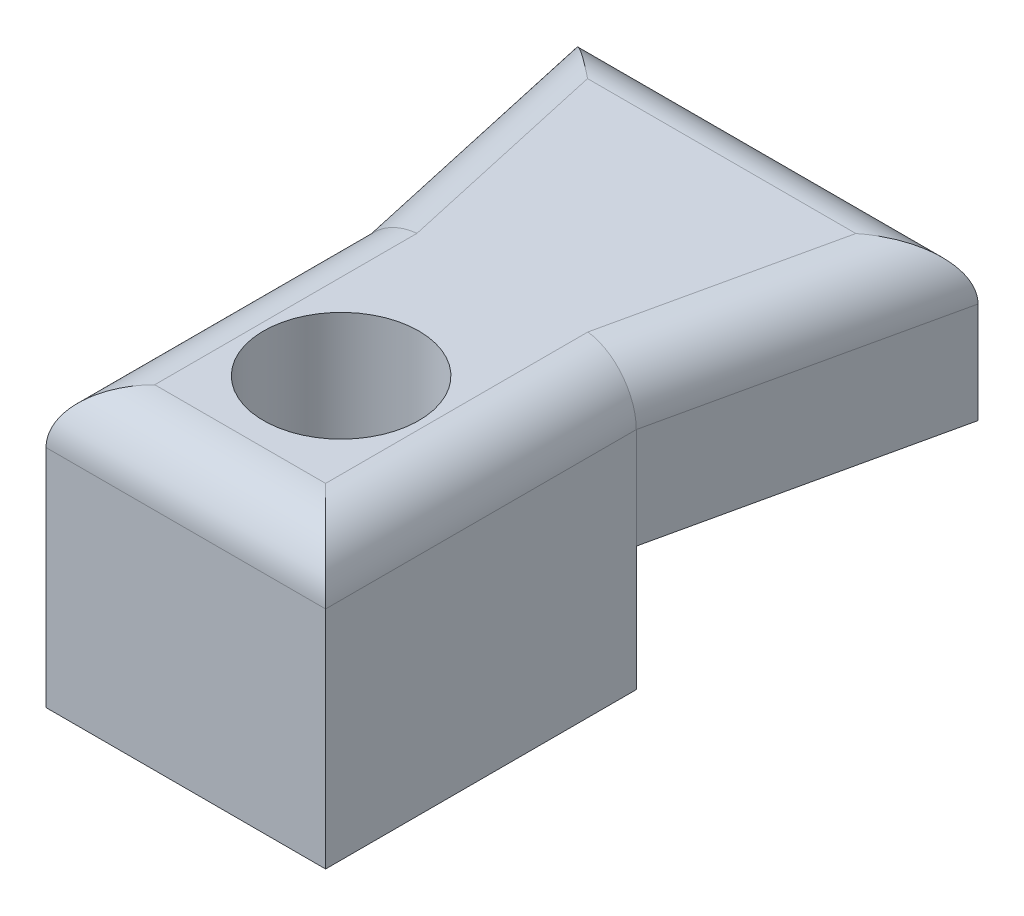
SolidWorks part; units mm, degrees
ref_plane "Front Plane" through (0, 0, 0) normal (0, 0, 1) x (1, 0, 0)
ref_plane "Top Plane" through (0, 0, 0) normal (0, 1, 0) x (1, 0, 0)
ref_plane "Right Plane" through (0, 0, 0) normal (1, 0, 0) x (0, 0, -1)
sketch "Sketch1" plane through (0, 0, 0) normal (0, 1, 0) x (1, 0, 0)
  line L0 (0, 0) -> (-2, 9)
  line L2 (0, 0) -> (0, -10)
  line L3 (0, -10) -> (9, -10)
  line L4 (9, 0) -> (9, -10)
  line L5 (-2, 9) -> (11, 9)
  line L6 (11, 9) -> (9, 0)
  dimension "D1" = 10
  dimension "D2" = 9
  dimension "D3" = 13
  dimension "D4" = 9
extrude "Boss-Extrude2" add sketch "Sketch1" along normal blind 5
sketch "Sketch3" plane through (0, 0, 0) normal (0, -1, 0) x (1, 0, 0)
  line L0 (0, 0) -> (0, 10) construction
  line L1 (9, 0) -> (0, 0)
  line L2 (9, 0) -> (9, 10)
  line L3 (9, 10) -> (0, 10)
  line L4 (0, 0) -> (0, 10)
extrude "Boss-Extrude3" add sketch "Sketch3" along normal blind 4
sketch "Sketch4" plane through (0, -4, 0) normal (0, -1, 0) x (1, 0, 0)
  line L0 (0, 0) -> (9, 10) construction
  circle A0 centre (4.5, 5) radius 2.5
extrude "Cut-Extrude1" cut sketch "Sketch4" against normal through all
fillet "Fillet1" radius 1.75 6 edges at (4.5, 5, -9) (10, 5, -4.5) (-1, 5, -4.5) (0, 5, 5) (9, 5, 5) (4.5, 5, 10)
